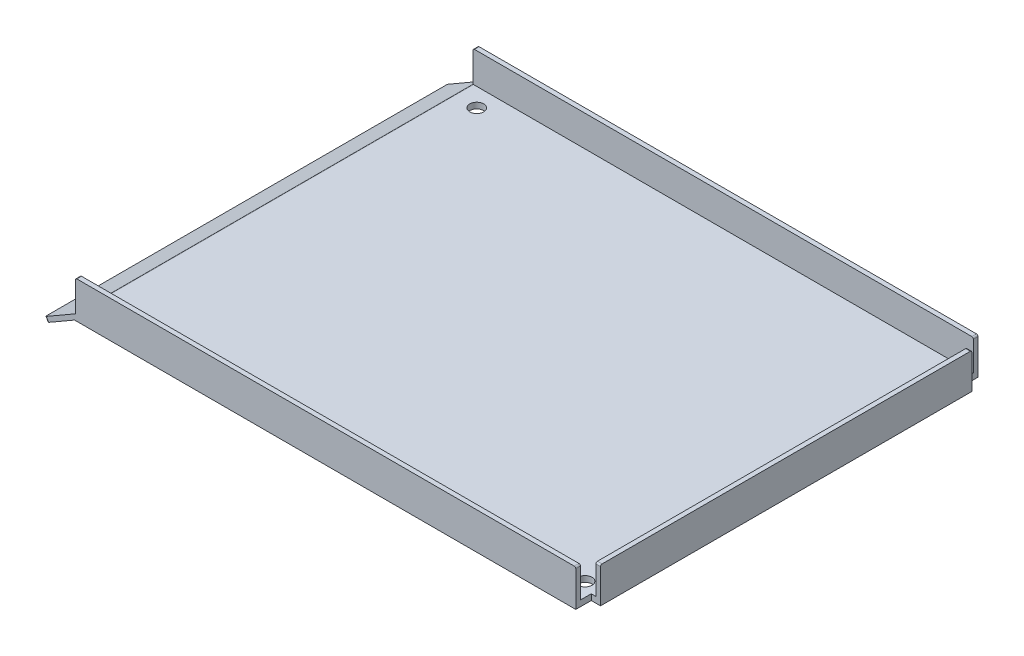
SolidWorks part; units mm, degrees
ref_plane "Front Plane" through (0, 0, 0) normal (0, 0, 1) x (1, 0, 0)
ref_plane "Top Plane" through (0, 0, 0) normal (0, 1, 0) x (1, 0, 0)
ref_plane "Right Plane" through (0, 0, 0) normal (1, 0, 0) x (0, 0, -1)
sketch "Sketch1" plane through (0, 0, 0) normal (0, 0, 1) x (1, 0, 0)
  line L0 (-4.8577, 2.3269) -> (-14.6384, -3.3201)
  line L1 (-4.8577, 2.3269) -> (158.3616, 2.3269)
  line L3 (-5.1384, 0.4327) -> (159.8616, 0.4327)
  line L6 (159.8616, 0.4327) -> (159.8616, 11.9327)
  line L7 (159.8616, 11.9327) -> (158.3616, 11.9327)
  line L8 (158.3616, 2.3269) -> (158.3616, 11.9327)
  line L9 (-14.6384, -3.3201) -> (-13.8884, -4.6191)
  line L10 (-13.8884, -4.6191) -> (-5.1384, 0.4327)
  dimension "D1" = 1.5
  dimension "D2" = 1.5
  dimension "D3" = 11.5
  dimension "D4" = 165
  dimension "D5" = 30
  dimension "D6" = 9.5
extrude "Boss-Extrude1" add sketch "Sketch1" along normal blind 130
sketch "Sketch3" plane through (0, 0.4327, 0) normal (0, -1, 0) x (1, 0, 0)
  line L1 (159.8616, 130) -> (156.8616, 130)
  line L2 (159.8616, 130) -> (159.8616, 125)
  line L3 (159.8616, 125) -> (156.8616, 125)
  line L4 (156.8616, 130) -> (156.8616, 125)
  line L5 (159.8616, 0) -> (156.8616, 0)
  line L6 (159.8616, 0) -> (159.8616, 5)
  line L7 (159.8616, 5) -> (156.8616, 5)
  line L8 (156.8616, 0) -> (156.8616, 5)
  dimension "D1" = 3
  dimension "D2" = 5
  dimension "D3" = 3
  dimension "D4" = 5
extrude "Cut-Extrude1" cut sketch "Sketch3" against normal through all
sketch "Sketch4" plane through (0, 2.3269, 0) normal (0, 1, 0) x (1, 0, 0)
  line L0 (-4.8577, -130) -> (-4.8577, 0) construction
  line L1 (156.8616, -130) -> (-4.8577, -130)
  line L2 (156.8616, -130) -> (156.8616, -128.5)
  line L3 (156.8616, -128.5) -> (-4.8577, -128.5)
  line L4 (-4.8577, -130) -> (-4.8577, -128.5)
  line L5 (156.8616, -5) -> (156.8616, 0) construction
  line L6 (-4.8577, 0) -> (156.8616, 0)
  line L7 (-4.8577, 0) -> (-4.8577, -1.5)
  line L8 (-4.8577, -1.5) -> (156.8616, -1.5)
  line L9 (156.8616, 0) -> (156.8616, -1.5)
  dimension "D1" = 1.5
  dimension "D2" = 1.5
extrude "Boss-Extrude2" add sketch "Sketch4" along normal blind 10
sketch "Sketch5" plane through (0, 2.3269, 0) normal (0, 1, 0) x (1, 0, 0)
  line L0 (-4.8577, -130) -> (156.8616, -130) construction
  line L1 (156.8616, 0) -> (-4.8577, 0) construction
  line L2 (159.8616, -125) -> (159.8616, -5) construction
  circle A0 centre (2.3616, -122.5) radius 2.25
  circle A1 centre (2.3616, -7.5) radius 2.25
  circle A2 centre (152.3616, -7.5) radius 2.25
  circle A3 centre (152.3616, -122.5) radius 2.25
  point P8 (0, 0)
  point P9 (0, 0)
  point P10 (0, 0)
  point P11 (0, 0)
  dimension "D5" = 4.5
  dimension "D1" = 7.5
  dimension "D2" = 7.5
  dimension "D3" = 150
  dimension "D4" = 7.5
extrude "Cut-Extrude2" cut sketch "Sketch5" against normal through all
fillet "Fillet1" radius 0.5 9 edges at (156.8616, 12.3269, 0.75) (159.1116, 11.9327, 5) (156.8616, 12.3269, 129.25) (159.1116, 11.9327, 125) (-4.8577, 12.3269, 0.75) (-4.8577, 12.3269, 129.25) (-14.2634, -3.9696, 130) (-4.8577, 2.3269, 65) (-14.2634, -3.9696, 0)
